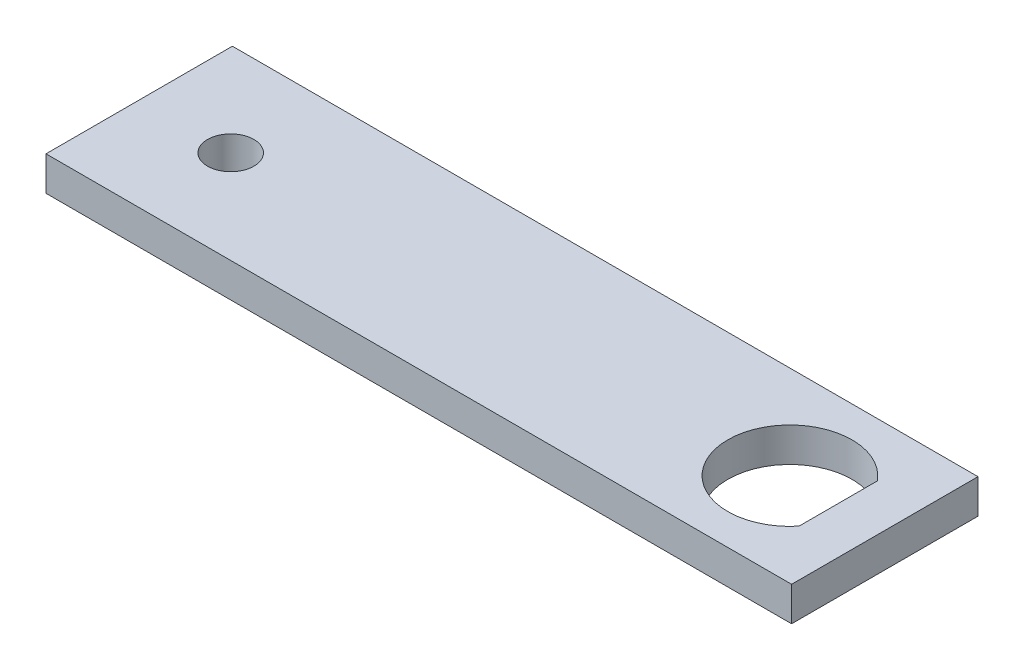
SolidWorks part; units mm, degrees
ref_plane "Front Plane" through (0, 0, 0) normal (0, 0, 1) x (1, 0, 0)
ref_plane "Top Plane" through (0, 0, 0) normal (0, 1, 0) x (1, 0, 0)
ref_plane "Right Plane" through (0, 0, 0) normal (1, 0, 0) x (0, 0, -1)
sketch "Sketch1" plane through (0, 0, 0) normal (0, 1, 0) x (1, 0, 0)
  line L0 (0, 9.525) -> (9.35, 9.525) construction
  line L1 (0, 0) -> (76.2, 0)
  line L2 (0, 0) -> (0, 19.05)
  line L3 (0, 19.05) -> (76.2, 19.05)
  line L4 (76.2, 0) -> (76.2, 19.05)
  line L5 (71.433, 13.5235) -> (71.433, 5.5265)
  circle A0 centre (9.35, 9.525) radius 2.37
  arc A1 (71.433, 13.5235) -> (71.433, 5.5265) centre (66.5, 9.525) ccw
  dimension "D3" = 4.74
  dimension "D5" = 12.7
  dimension "D1" = 19.05
  dimension "D2" = 76.2
  dimension "D4" = 9.35
  dimension "D6" = 57.15
extrude "Boss-Extrude1" add sketch "Sketch1" along normal blind 3.5
